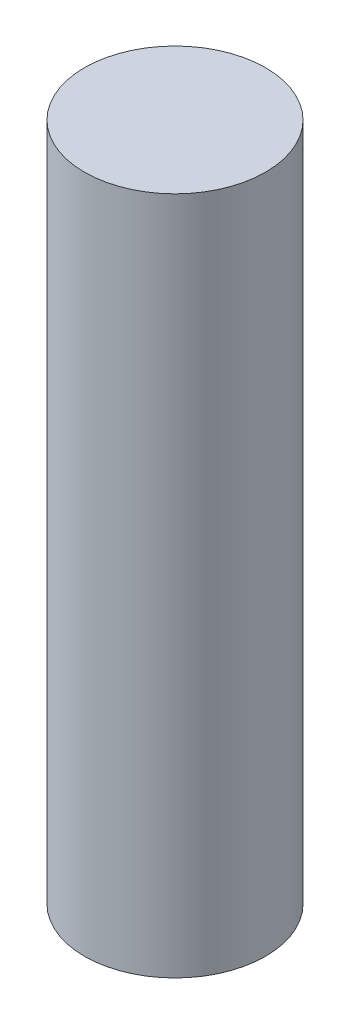
SolidWorks part; units mm, degrees
ref_plane "Front" through (0, 0, 0) normal (0, 0, 1) x (1, 0, 0)
ref_plane "Top" through (0, 0, 0) normal (0, 1, 0) x (1, 0, 0)
ref_plane "Right" through (0, 0, 0) normal (1, 0, 0) x (0, 0, -1)
sketch "Sketch1" plane through (0, 0, 0) normal (0, 1, 0) x (1, 0, 0)
  circle A0 centre (0, 0) radius 2
  dimension "D1" = 4
extrude "Boss-Extrude1" add sketch "Sketch1" along normal blind 15
